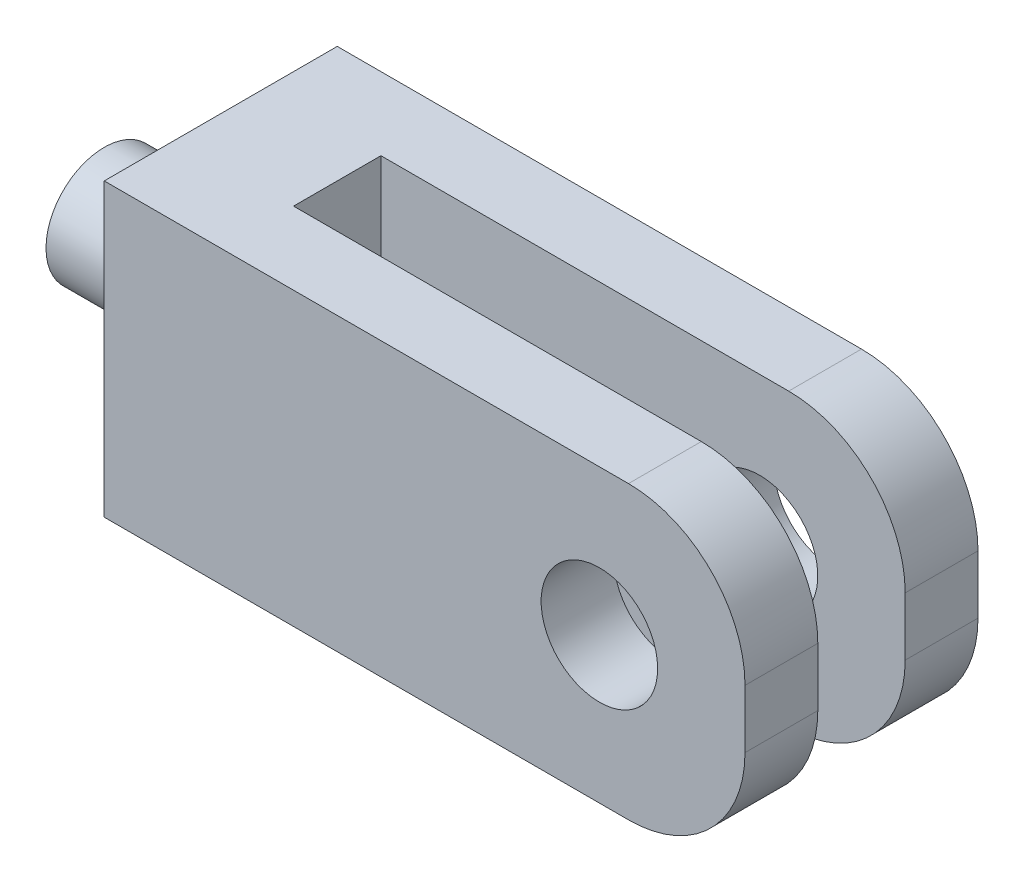
SolidWorks part; units mm, degrees
ref_plane "Front Plane" through (0, 0, 0) normal (0, 0, 1) x (1, 0, 0)
ref_plane "Top Plane" through (0, 0, 0) normal (0, 1, 0) x (1, 0, 0)
ref_plane "Right Plane" through (0, 0, 0) normal (1, 0, 0) x (0, 0, -1)
sketch "Sketch1" plane through (0, 0, 0) normal (0, 0, 1) x (1, 0, 0)
  line L1 (-55, -25) -> (55, -25)
  line L2 (-55, -25) -> (-55, 25)
  line L3 (-55, 25) -> (55, 25)
  line L4 (55, -25) -> (55, 25)
  line L5 (-55, -25) -> (55, 25) construction
  line L6 (-55, 25) -> (55, -25) construction
  point P0 (0, 0)
  dimension "D1" = 110
  dimension "D2" = 50
extrude "Boss-Extrude1" add sketch "Sketch1" along normal blind 40
sketch "Sketch2" plane through (55, 0, 0) normal (1, 0, 0) x (0, 0, -1)
  line L0 (-40, 25) -> (0, 25) construction
  line L1 (-12.5, -25) -> (-27.5, -25)
  line L2 (-12.5, -25) -> (-12.5, 25)
  line L3 (-12.5, 25) -> (-27.5, 25)
  line L4 (-27.5, -25) -> (-27.5, 25)
  line L5 (-12.5, -25) -> (-27.5, 25) construction
  line L6 (-12.5, 25) -> (-27.5, -25) construction
  point P0 (-20, 0)
  dimension "D1" = 15
  dimension "D2" = 20
extrude "Cut-Extrude1" cut sketch "Sketch2" against normal blind 90
fillet "Fillet1" radius 20 4 edges at (55, -25, 6.25) (55, -25, 33.75) (55, 25, 6.25) (55, 25, 33.75)
sketch "Sketch3" plane through (0, 0, 40) normal (0, 0, 1) x (1, 0, 0)
  circle A0 centre (30, 0) radius 10
  dimension "D1" = 20
  dimension "D2" = 30
extrude "Cut-Extrude2" cut sketch "Sketch3" against normal blind 90
sketch "Sketch4" plane through (-55, 0, 0) normal (-1, 0, 0) x (0, 0, 1)
  line L0 (40, 25) -> (0, -25) construction
  circle A0 centre (20, 0) radius 10
  dimension "D1" = 20
extrude "Boss-Extrude2" add sketch "Sketch4" along normal blind 20
